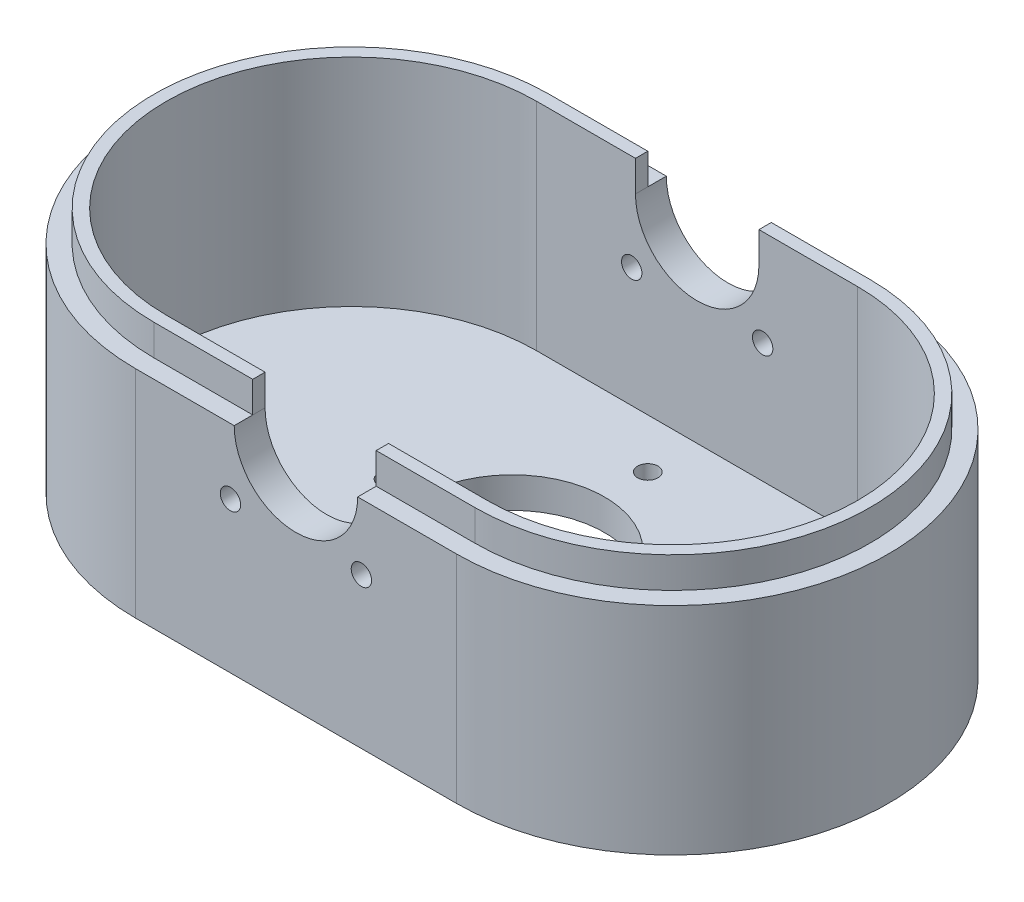
SolidWorks part; units mm, degrees
ref_plane "정면" through (0, 0, 0) normal (0, 0, 1) x (1, 0, 0)
ref_plane "윗면" through (0, 0, 0) normal (0, 1, 0) x (1, 0, 0)
ref_plane "우측면" through (0, 0, 0) normal (1, 0, 0) x (0, 0, -1)
sketch "스케치1" plane through (0, 0, 0) normal (0, 1, 0) x (1, 0, 0)
  line L0 (0, -1046.8615) -> (0, -35) construction
  line L1 (-26, 35) -> (26, 35)
  line L3 (-26, -35) -> (26, -35)
  line L5 (-26, 35) -> (26, -35) construction
  line L6 (-26, -35) -> (26, 35) construction
  line L7 (0, 0) -> (50000, 0) construction
  line L8 (0, 35) -> (0, 50000) construction
  arc A1 (26, -35) -> (26, 35) centre (26, 0) ccw
  arc A2 (-26, 35) -> (-26, -35) centre (-26, 0) ccw
  point P0 (0, 0)
  dimension "D3" = 70
  dimension "D1" = 52
  dimension "D2" = 70
extrude "보스-돌출1" add sketch "스케치1" along normal blind 35
sketch "스케치2" plane through (0, 35, 0) normal (0, 1, 0) x (1, 0, 0)
  line L4 (26, 30) -> (-26, 30)
  line L5 (-26, -30) -> (26, -30)
  line L6 (26, 30) -> (-26, 30)
  line L7 (-26, -30) -> (26, -30)
  arc A4 (26, -30) -> (26, 30) centre (26, 0) ccw
  arc A5 (-26, 30) -> (-26, -30) centre (-26, 0) ccw
  arc A6 (26, -30) -> (26, 30) centre (26, 0) ccw
  arc A7 (-26, 30) -> (-26, -30) centre (-26, 0) ccw
  dimension "D1" = 5
extrude "컷-돌출1" cut sketch "스케치2" against normal blind 30
sketch "스케치3" plane through (0, 0, 35) normal (0, 0, 1) x (1, 0, 0)
  line L0 (0, 0) -> (0, 50000) construction
  line L1 (-26, 35) -> (26, 35) construction
  line L2 (0, 35) -> (35355.3391, 35390.3391) construction
  line L3 (0, 35) -> (35355.3391, -35320.3391) construction
  circle A0 centre (0, 35) radius 10
  circle A1 centre (0, 35) radius 15 construction
  circle A2 centre (10.6066, 24.3934) radius 2 construction
  circle A5 centre (-10.6066, 24.3934) radius 2 construction
  dimension "D1" = 20
  dimension "D2" = 30
  dimension "D3" = 45
  dimension "D4" = 4
  dimension "D5" = 4
extrude "컷-돌출2" cut sketch "스케치3" against normal through all both and the other way through all
sketch "스케치4" plane through (0, 5, 0) normal (0, 1, 0) x (1, 0, 0)
  line L0 (0, 0) -> (0, 50000) construction
  line L1 (0, 0) -> (50000, 0) construction
  circle A0 centre (0, 0) radius 15
  circle A2 centre (0, 22) radius 2 construction
  circle A3 centre (-20, 0) radius 2 construction
  circle A4 centre (0, -22) radius 2 construction
  circle A5 centre (50, 0) radius 2 construction
  dimension "D1" = 30
  dimension "D2" = 20
  dimension "D3" = 4
  dimension "D4" = 4
  dimension "D5" = 4
  dimension "D8" = 4
  dimension "D6" = 22
  dimension "D7" = 22
  dimension "D9" = 50
extrude "컷-돌출3" cut sketch "스케치4" against normal up to next
sketch "스케치5" plane through (0, 35, 0) normal (0, 1, 0) x (1, 0, 0)
  line L16 (-10, 32) -> (-26, 32)
  line L17 (-26, -32) -> (-10, -32)
  line L20 (-26, -30) -> (-10, -30)
  line L21 (-10, 30) -> (-26, 30)
  line L22 (-26, -30) -> (-10, -30)
  line L23 (-10, 30) -> (-26, 30)
  line L26 (-10, 32) -> (-10, 30)
  line L27 (-10, -30) -> (-10, -32)
  line L37 (10, -32) -> (26, -32)
  line L38 (26, 32) -> (10, 32)
  line L39 (26, 30) -> (10, 30)
  line L40 (10, -30) -> (26, -30)
  line L41 (26, 30) -> (10, 30)
  line L42 (10, -30) -> (26, -30)
  line L43 (10, 32) -> (10, 30)
  line L44 (10, -30) -> (10, -32)
  arc A17 (-26, 32) -> (-26, -32) centre (-26, 0) ccw
  arc A19 (-26, 30) -> (-26, -30) centre (-26, 0) ccw
  arc A22 (-26, 30) -> (-26, -30) centre (-26, 0) ccw
  arc A27 (26, -32) -> (26, 32) centre (26, 0) ccw
  arc A28 (26, -30) -> (26, 30) centre (26, 0) ccw
  arc A29 (26, -30) -> (26, 30) centre (26, 0) ccw
  dimension "D1" = 0
  dimension "D2" = 2
  dimension "D4" = 0
  dimension "D5" = 2
extrude "보스-돌출2" add sketch "스케치5" along normal blind 5
hole_wizard "M4 나사 구멍1" positions "스케치6" profile "스케치7" tap size "M4" standard "ISO" end condition up to next
sketch "스케치6" plane through (0, 0, 35) normal (0, 0, 1) x (1, 0, 0)
  point P0 (-10.6066, 24.3934)
  point P3 (10.6066, 24.3934)
sketch "스케치7" plane through (-10.6066, 24.3934, 35) normal (1, 0, 0) x (0, -1, 0)
  line L0 (0, 0) -> (0, 5)
  line L1 (0, 5) -> (1.65, 5)
  line L2 (1.65, 5) -> (1.65, 0)
  line L5 (1.65, 0) -> (0, 0)
  line L11 (0, -6.35) -> (0, 107.95) construction
  dimension "관통 탭 드릴 지름" = 3.3
  dimension "관통 탭 드릴 깊이" = 5
cosmetic thread "구멍 나사산1" parameters "D2"=4
cosmetic thread "구멍 나사산2" parameters "D2"=4
hole_wizard "M4 나사 구멍2" positions "스케치8" profile "스케치9" tap size "M4" standard "ISO" end condition up to next
sketch "스케치8" plane through (0, 0, -35) normal (0, 0, -1) x (-1, 0, 0)
  point P0 (-10.6066, 24.3934)
  point P3 (10.6066, 24.3934)
sketch "스케치9" plane through (10.6066, 24.3934, -35) normal (1, 0, 0) x (0, 1, 0)
  line L0 (0, 0) -> (0, 5)
  line L1 (0, 5) -> (1.65, 5)
  line L2 (1.65, 5) -> (1.65, 0)
  line L5 (1.65, 0) -> (0, 0)
  line L11 (0, -6.35) -> (0, 107.95) construction
  dimension "관통 탭 드릴 지름" = 3.3
  dimension "관통 탭 드릴 깊이" = 5
cosmetic thread "구멍 나사산3" parameters "D2"=4
cosmetic thread "구멍 나사산4" parameters "D2"=4
hole_wizard "M4 나사 구멍3" positions "스케치10" profile "스케치11" tap size "M4" standard "ISO" end condition through all
sketch "스케치10" plane through (0, 5, 0) normal (0, 1, 0) x (1, 0, 0)
  point P0 (0, 22)
  point P3 (-20, 0)
  point P6 (50, 0)
  point P9 (0, -22)
sketch "스케치11" plane through (0, 5, -22) normal (1, 0, 0) x (0, 0, 1)
  line L0 (0, 0) -> (0, 5)
  line L1 (0, 5) -> (1.65, 5)
  line L2 (1.65, 5) -> (1.65, 0)
  line L5 (1.65, 0) -> (0, 0)
  line L11 (0, -6.35) -> (0, 107.95) construction
  dimension "관통 탭 드릴 지름" = 3.3
  dimension "관통 탭 드릴 깊이" = 5
cosmetic thread "구멍 나사산5" parameters "D2"=4
cosmetic thread "구멍 나사산6" parameters "D2"=4
cosmetic thread "구멍 나사산7" parameters "D2"=4
cosmetic thread "구멍 나사산8" parameters "D2"=4
